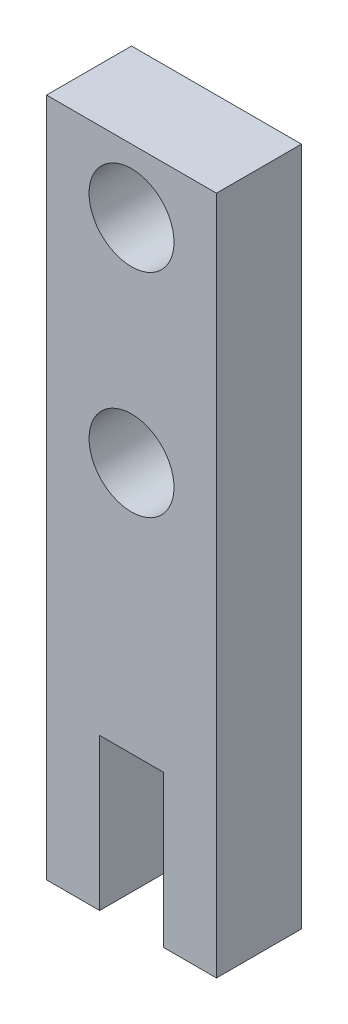
SolidWorks part; units mm, degrees
ref_plane "Front Plane" through (0, 0, 0) normal (0, 0, 1) x (1, 0, 0)
ref_plane "Top Plane" through (0, 0, 0) normal (0, 1, 0) x (1, 0, 0)
ref_plane "Right Plane" through (0, 0, 0) normal (1, 0, 0) x (0, 0, -1)
sketch "Sketch1" plane through (0, 0, 0) normal (0, 0, 1) x (1, 0, 0)
  line L1 (0, 0) -> (50.8, 0)
  line L2 (0, 0) -> (0, 203.2)
  line L3 (0, 203.2) -> (50.8, 203.2)
  line L4 (50.8, 0) -> (50.8, 203.2)
  dimension "D1" = 203.2
  dimension "D2" = 50.8
extrude "Boss-Extrude1" add sketch "Sketch1" along normal blind 25.4
sketch "Sketch2" plane through (0, 0, 25.4) normal (0, 0, 1) x (1, 0, 0)
  line L0 (50.8, 203.2) -> (0, 203.2) construction
  line L1 (0, 203.2) -> (0, 0) construction
  line L2 (0, 0) -> (50.8, 0) construction
  circle A0 centre (25.4, 184.15) radius 12.7
  circle A1 centre (25.4, 120.65) radius 12.7
  dimension "D1" = 25.4
  dimension "D2" = 25.4
  dimension "D3" = 19.05
  dimension "D4" = 25.4
  dimension "D5" = 25.4
  dimension "D6" = 120.65
extrude "Cut-Extrude1" cut sketch "Sketch2" against normal through all and the other way through all
sketch "Sketch3" plane through (0, 0, 25.4) normal (0, 0, 1) x (1, 0, 0)
  line L0 (0, 0) -> (50.8, 0) construction
  line L1 (0, 203.2) -> (0, 0) construction
  circle A0 centre (25.4, 25.4) radius 6.35
  dimension "D1" = 12.7
  dimension "D2" = 25.4
  dimension "D3" = 25.4
extrude "Cut-Extrude2" cut sketch "Sketch3" against normal through all
sketch "Sketch4" plane through (0, 0, 25.4) normal (0, 0, 1) x (1, 0, 0)
  line L0 (0, 0) -> (50.8, 0) construction
  line L1 (34.925, 0) -> (15.875, 0)
  line L2 (34.925, 0) -> (34.925, 45.3498)
  line L3 (34.925, 45.3498) -> (15.875, 45.3498)
  line L4 (15.875, 0) -> (15.875, 45.3498)
  line L5 (0, 203.2) -> (0, 0) construction
  dimension "D1" = 19.05
  dimension "D2" = 15.875
extrude "Cut-Extrude3" cut sketch "Sketch4" against normal through all
